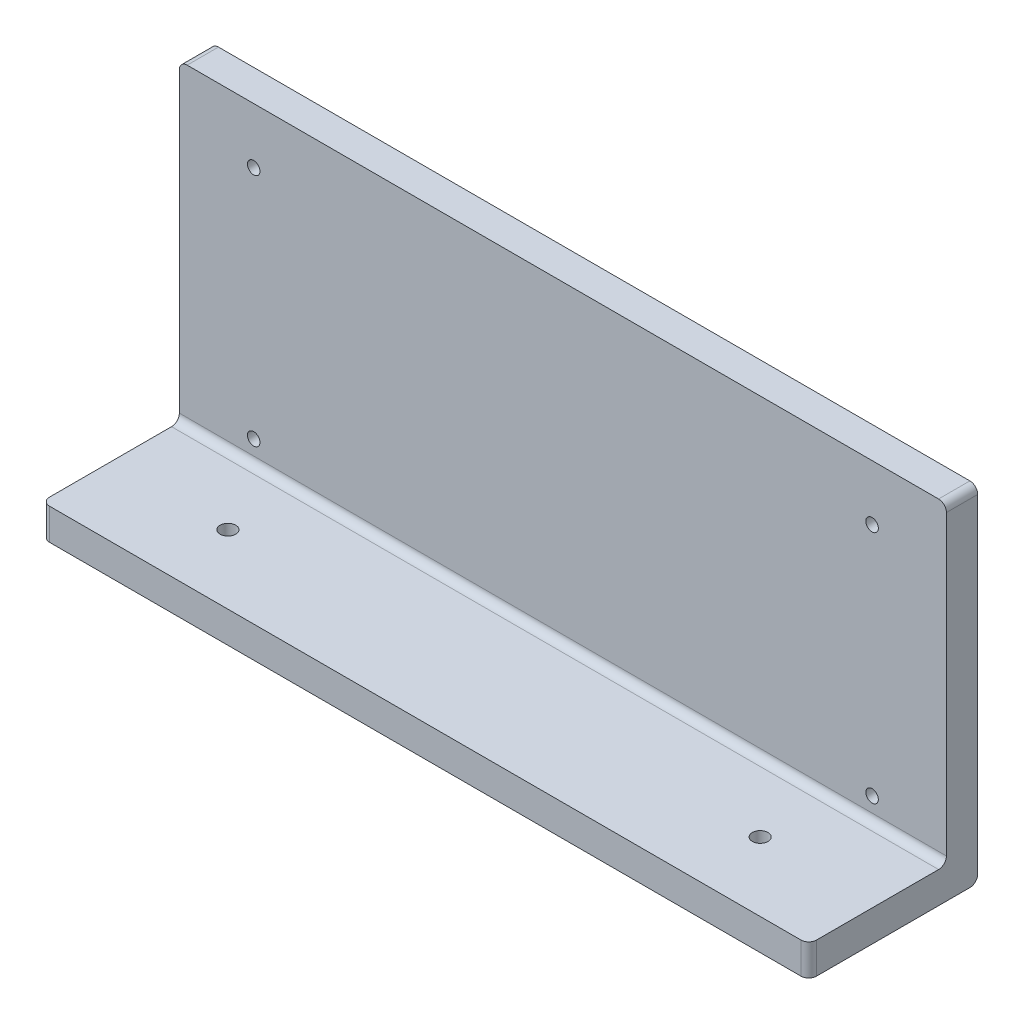
SolidWorks part; units mm, degrees
ref_plane "Front Plane" through (0, 0, 0) normal (0, 0, 1) x (1, 0, 0)
ref_plane "Top Plane" through (0, 0, 0) normal (0, 1, 0) x (1, 0, 0)
ref_plane "Right Plane" through (0, 0, 0) normal (1, 0, 0) x (0, 0, -1)
sketch "Sketch1" plane through (0, 0, 0) normal (0, 1, 0) x (1, 0, 0)
  line L1 (-49, -10.795) -> (49, -10.795)
  line L2 (-49, -10.795) -> (-49, 10.795)
  line L3 (-49, 10.795) -> (49, 10.795)
  line L4 (49, -10.795) -> (49, 10.795)
  line L5 (-49, -10.795) -> (49, 10.795) construction
  line L6 (-49, 10.795) -> (49, -10.795) construction
  point P0 (0, 0)
  dimension "D1" = 98
  dimension "D2" = 21.59
extrude "Boss-Extrude1" add sketch "Sketch1" along normal blind 4
sketch "Sketch2" plane through (0, 4, 0) normal (0, 1, 0) x (1, 0, 0)
  line L0 (-49, 10.795) -> (-49, -10.795) construction
  line L1 (49, 10.795) -> (-49, 10.795)
  line L2 (49, 10.795) -> (49, 6.795)
  line L3 (49, 6.795) -> (-49, 6.795)
  line L4 (-49, 10.795) -> (-49, 6.795)
  dimension "D1" = 4
extrude "Boss-Extrude2" add sketch "Sketch2" along normal blind 40
sketch "Sketch3" plane through (0, 0, -6.795) normal (0, 0, 1) x (1, 0, 0)
  line L0 (-49, 44) -> (49, 44) construction
  line L1 (-39.5, 36.9041) -> (39.5, 6.9041) construction
  line L2 (-39.5, 6.9041) -> (39.5, 36.9041) construction
  circle A0 centre (-39.5, 6.9041) radius 0.8
  circle A1 centre (-39.5, 36.9041) radius 0.8
  circle A2 centre (39.5, 36.9041) radius 0.8
  circle A3 centre (39.5, 6.9041) radius 0.8
extrude "Cut-Extrude1" cut sketch "Sketch3" against normal blind 21
fillet "Fillet1" radius 1 6 edges at (0, 0, -10.795) (0, 4, -6.795) (49, 2, 10.795) (-49, 44, -8.795) (49, 44, -8.795) (-49, 2, 10.795)
sketch "Sketch4" plane through (0, 4, 0) normal (0, 1, 0) x (1, 0, 0)
  line L0 (-49, -2) -> (49, -2) construction
  line L1 (-49, 5.795) -> (-49, -9.795) construction
  line L2 (49, -9.795) -> (49, 5.795) construction
  line L3 (-48, -10.795) -> (48, -10.795) construction
  line L4 (0, -11.8745) -> (0, 11.8745) construction
  circle A0 centre (-34, -2) radius 1
  circle A1 centre (34, -2) radius 1
  dimension "D1" = 15
  dimension "D2" = 8.795
  dimension "D3" = 68
extrude "Cut-Extrude2" cut sketch "Sketch4" against normal blind 21
